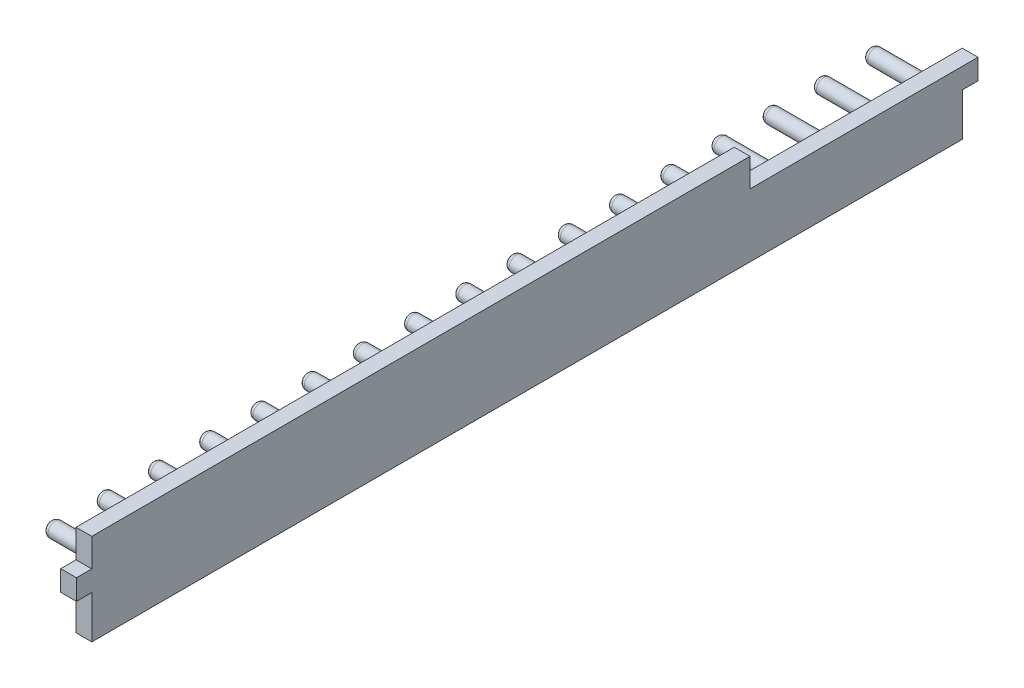
SolidWorks part; units mm, degrees
ref_plane "Front Plane" through (0, 0, 0) normal (0, 0, 1) x (1, 0, 0)
ref_plane "Top Plane" through (0, 0, 0) normal (0, 1, 0) x (1, 0, 0)
ref_plane "Right Plane" through (0, 0, 0) normal (1, 0, 0) x (0, 0, -1)
sketch "Sketch1" plane through (0, 0, 0) normal (0, 0, 1) x (1, 0, 0)
  line B0 (0, 7.95) -> (2.04, 7.95)
  line B1 (6.1524, 4.048) -> (6.1524, -4.048)
  line B2 (2.04, -7.95) -> (0, -7.95)
  line B3 (0, -7.95) -> (0, 7.95)
  line B4 (2.04, 7.95) -> (6.1524, 4.048)
  line B5 (6.1524, -4.048) -> (2.04, -7.95)
sketch_block_instance "Extrusion Profile-1"
sketch_block "Extrusion Profile" parameters "D1"=8.44, "D2"=2.6, "D3"=6, "D4"=16.7, "D6"=5.6686, "D7"=2.0404, "D8"=8.0963, "D9"=15.9, "D5"=2.4157
extrude "Boss-Extrude1" add sketch "Sketch1" along normal blind 340
sketch "Sketch2" plane through (0, 0, 0) normal (-1, 0, 0) x (0, 0, 1)
  circle A0 centre (10, 0) radius 2.9
  circle A1 centre (30, 0) radius 2.9
  circle A2 centre (50, 0) radius 2.9
  circle A3 centre (70, 0) radius 2.9
  circle A4 centre (90, 0) radius 2.9
  circle A5 centre (110, 0) radius 2.9
  circle A6 centre (130, 0) radius 2.9
  circle A7 centre (150, 0) radius 2.9
  circle A8 centre (170, 0) radius 2.9
  circle A9 centre (190, 0) radius 2.9
  circle A10 centre (210, 0) radius 2.9
  circle A11 centre (230, 0) radius 2.9
  circle A12 centre (250, 0) radius 2.9
  dimension "D2" = 5.8
  dimension "D1" = 10
  dimension "D4" = 20
  dimension "D3" = 13
extrude "Boss-Extrude2" add sketch "Sketch2" along normal blind 20
sketch "Sketch3" [suppressed] plane through (0, 0, 0) normal (-1, 0, 0) x (0, 0, 1)
  line L0 (190, 0) -> (210, 0) construction
  line L1 (200, 0) -> (200, 7.95) construction
  line L2 (260, 7.95) -> (0, 7.95) construction
  line L3 (200, 7.95) -> (200, 7)
  line L4 (200, 7) -> (100, 7)
  line L5 (100, 7) -> (100, 7.95)
  line L6 (100, 7.95) -> (200, 7.95)
  line L7 (90, 0) -> (110, 0) construction
  line L8 (100, 0) -> (100, 7) construction
  dimension "D1" = 7
extrude "Cut-Extrude1" [suppressed] cut sketch "Sketch3" against normal through all
chamfer "Chamfer1" [suppressed] distance 3 angle 45
fillet "Fillet1" [suppressed] radius 8
sketch "Sketch4" plane through (0, 0, 0) normal (-1, 0, 0) x (0, 0, 1)
  line L0 (250, 0) -> (230, 0) construction
  line L1 (250, 0) -> (270, 0) construction
  circle A0 centre (270, 0) radius 2.9
  circle A1 centre (250, 0) radius 2.9 construction
  circle A2 centre (290, 0) radius 2.9
  circle A3 centre (310, 0) radius 2.9
  circle A4 centre (330, 0) radius 2.9
  dimension "D2" = 20
  dimension "D1" = 4
extrude "Boss-Extrude3" add sketch "Sketch4" along normal blind 20
sketch "Sketch5" plane through (0, 0, 340) normal (0, 0, 1) x (1, 0, 0)
  line L5 (0, -7.95) -> (0, -20.95)
  line L6 (0, -20.95) -> (6.1524, -20.95)
  line L7 (6.1524, -20.95) -> (6.1524, -4.048)
  line L8 (0, -7.95) -> (2.04, -7.95) construction
  line L9 (0, -7.95) -> (2.04, -7.95)
  line L10 (2.04, -7.95) -> (6.1524, -4.048)
  line L11 (0, 7.95) -> (0, 14.75)
  line L12 (0, 14.75) -> (6.1524, 14.75)
  line L13 (6.1524, 14.75) -> (6.1524, 4.048)
  line L14 (2.04, 7.95) -> (0, 7.95) construction
  line L15 (0, 7.95) -> (2.04, 7.95)
  line L16 (2.04, 7.95) -> (6.1524, 4.048)
  dimension "D1" = 13
  dimension "D2" = 6.8
extrude "Boss-Extrude4" add sketch "Sketch5" against normal up to surface (340 mm away) up to face at (2.7308, 0, 0)
sketch "Sketch7" plane through (0, 0, 340) normal (0, 0, 1) x (1, 0, 0)
  line L0 (6.1524, -20.95) -> (6.1524, 14.75) construction
  line L1 (6.1524, -4.25) -> (0, -4.25)
  line L2 (6.1524, -4.25) -> (6.1524, 3.75)
  line L3 (6.1524, 3.75) -> (0, 3.75)
  line L4 (0, -4.25) -> (0, 3.75)
  line L5 (0, 14.75) -> (0, -20.95) construction
  line L6 (0, -0.25) -> (6.1524, -0.25)
  line L8 (6.1524, 14.75) -> (0, 14.75) construction
  dimension "D1" = 8
  dimension "D2" = 15
extrude "Boss-Extrude5" add sketch "Sketch7" along normal blind 6
ref_plane "Plane1" through (0, 0, 170) normal (0, 0, 1) x (1, 0, 0)
mirror "Mirror1" about plane through (0, 0, 170) normal (0, 0, 1) of "Boss-Extrude5"
sketch "Sketch8" [suppressed] plane through (0, 0, 0) normal (-1, 0, 0) x (0, 0, 1)
  line L0 (0, 7) -> (90, 7)
  line L1 (0, 7.95) -> (0, -7.95) construction
  line L2 (90, 7) -> (90, 7.95)
  line L3 (340, 7.95) -> (0, 7.95) construction
  line L4 (90, 7.95) -> (0, 7.95)
  line L5 (0, 7.95) -> (0, 7)
  circle A0 centre (10, 0) radius 2.9 construction
  dimension "D1" = 7
  dimension "D2" = 90
extrude "Cut-Extrude2" [suppressed] cut sketch "Sketch8" against normal blind 5
fillet "Fillet2" radius 2 13 edges at (-20, -2.9, 10) (-20, -2.9, 250) (-20, -2.9, 230) (-20, -2.9, 210) (-20, -2.9, 190) (-20, -2.9, 170) (-20, -2.9, 150) (-20, -2.9, 130) (-20, -2.9, 110) (-20, -2.9, 90) (-20, -2.9, 70) (-20, -2.9, 50) (-20, -2.9, 30)
fillet "Fillet3" radius 2 4 edges at (-20, -2.9, 330) (-20, -2.9, 310) (-20, -2.9, 290) (-20, -2.9, 270)
sketch "Sketch9" plane through (6.1524, 0, 0) normal (1, 0, 0) x (0, 0, -1)
  line L0 (0, 14.75) -> (-340, 14.75) construction
  line L1 (-83, 3.75) -> (0, 3.75)
  line L2 (-83, 3.75) -> (-83, 14.75)
  line L3 (-83, 14.75) -> (0, 14.75)
  line L4 (0, 3.75) -> (0, 14.75)
  line L5 (0, 3.75) -> (0, 14.75) construction
  point P5 (0, 0)
  dimension "D1" = 83
  dimension "D2" = 11
extrude "Cut-Extrude3" cut sketch "Sketch9" against normal through all
